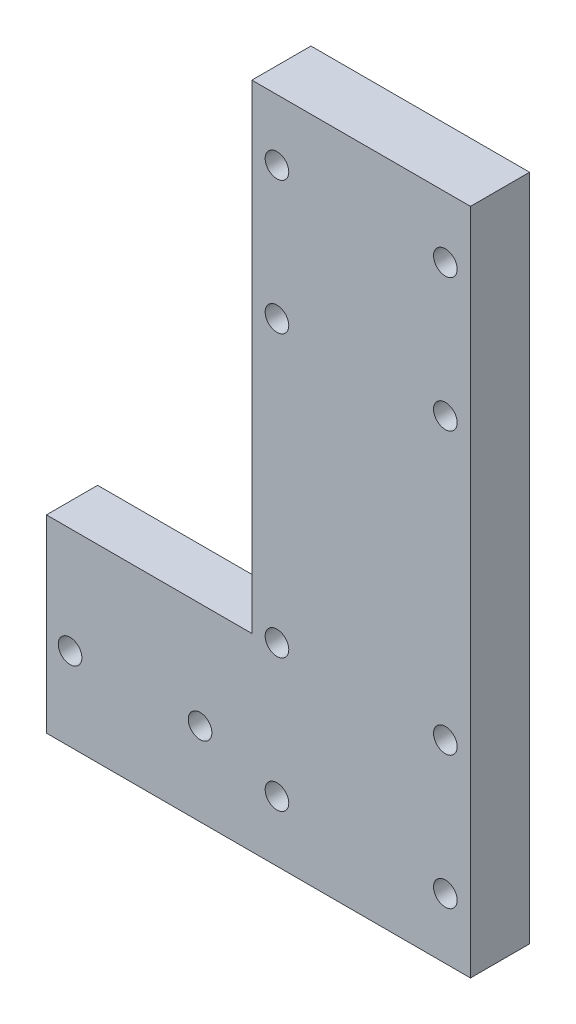
SolidWorks part; units mm, degrees
ref_plane "Płaszczyzna przednia" through (0, 0, 0) normal (0, 0, 1) x (1, 0, 0)
ref_plane "Płaszczyzna górna" through (0, 0, 0) normal (0, 1, 0) x (1, 0, 0)
ref_plane "Płaszczyzna prawa" through (0, 0, 0) normal (1, 0, 0) x (0, 0, -1)
sketch "Szkic2" plane through (0, 0, -3.8159) normal (0, 0, 1) x (1, 0, 0)
  line L0 (5.9823, 6.1884) -> (-6.3177, 6.1884) construction
  line L5 (-37.1341, 6.1884) -> (36.8659, 6.1884)
  line L6 (-37.1341, 6.1884) -> (-37.1341, -220.0116)
  line L7 (-37.1341, -220.0116) -> (36.8659, -220.0116)
  line L8 (36.8659, 6.1884) -> (36.8659, -220.0116)
  line L9 (-6.3177, -220.0116) -> (5.9823, -220.0116) construction
  dimension "D1" = 74
extrude "Dodanie-wyciągnięcie1" add sketch "Szkic2" along normal blind 20
sketch "Szkic3" plane through (-37.1341, 0, 0) normal (-1, 0, 0) x (0, 0, 1)
  line L1 (16.1841, -220.0116) -> (-1.1359, -220.0116)
  line L2 (16.1841, -220.0116) -> (16.1841, -156.0116)
  line L3 (16.1841, -156.0116) -> (-1.1359, -156.0116)
  line L4 (-1.1359, -220.0116) -> (-1.1359, -156.0116)
  dimension "D1" = 17.32
  dimension "D2" = 64
extrude "Dodanie-wyciągnięcie2" add sketch "Szkic3" along normal blind 69.53
sketch "Szkic4" plane through (0, 0, 16.1841) normal (0, 0, 1) x (1, 0, 0)
  circle A0 centre (-54.6677, -191.9069) radius 4
  circle A1 centre (-98.6677, -191.9069) radius 4
extrude "Wytnij-wyciągnięcie1" cut sketch "Szkic4" against normal blind 20
sketch "Szkic6" plane through (0, 0, -4.1159) normal (0, 0, 1) x (1, 0, 0)
  circle A0 centre (28.3659, -199.5069) radius 4
  circle A1 centre (-28.6341, -199.5069) radius 4
  circle A2 centre (-28.6341, -154.5069) radius 4
  circle A3 centre (28.3659, -154.5069) radius 4
extrude "Wytnij-wyciągnięcie3" cut sketch "Szkic6" along normal blind 21
sketch "Szkic7" plane through (0, 0, -3.8159) normal (0, 0, 1) x (1, 0, 0)
  circle A0 centre (28.3659, -14.5069) radius 4
  circle A1 centre (-28.6341, -14.5069) radius 4
  circle A2 centre (-28.6341, -59.5069) radius 4
  circle A3 centre (28.3659, -59.5069) radius 4
extrude "Wytnij-wyciągnięcie4" cut sketch "Szkic7" along normal blind 20
mirror "Lustro4" [suppressed]
delete or keep bodies "Obiekt-Usuń/zachowaj 1" [suppressed] type delete bodies bodies 107
